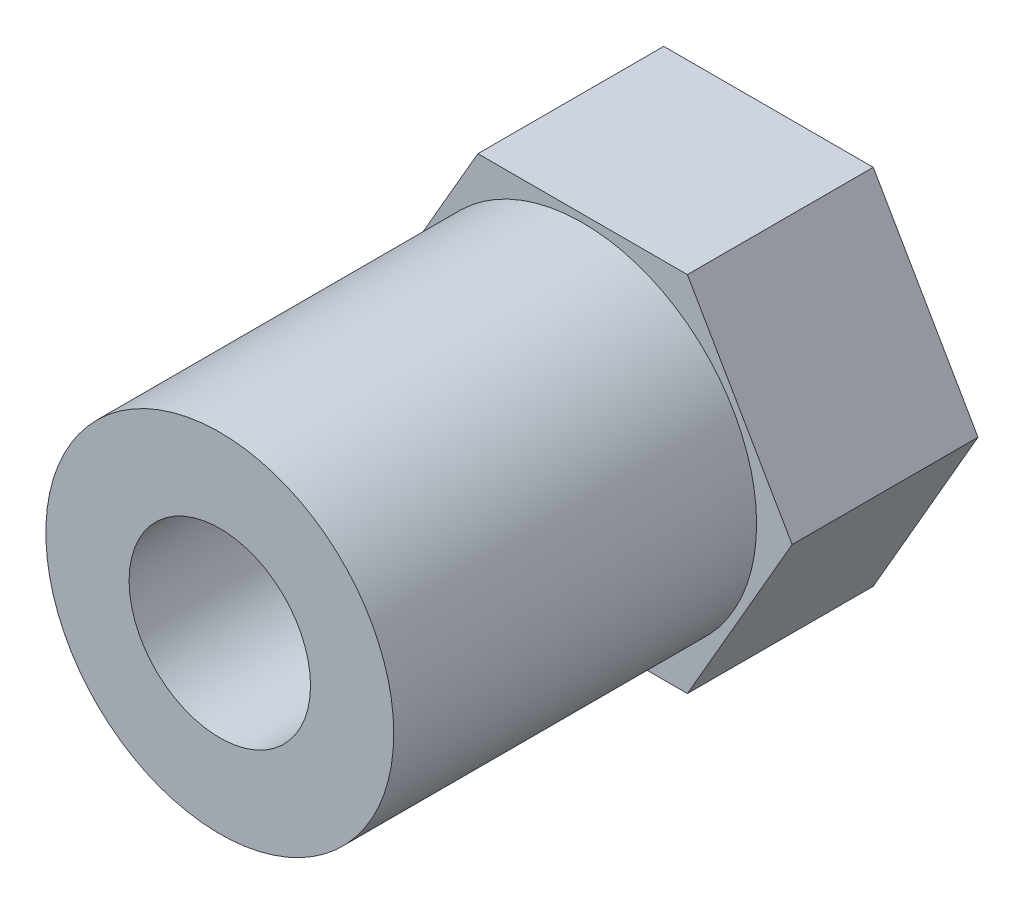
SolidWorks part; units mm, degrees
ref_plane "Front Plane" through (0, 0, 0) normal (0, 0, 1) x (1, 0, 0)
ref_plane "Top Plane" through (0, 0, 0) normal (0, 1, 0) x (1, 0, 0)
ref_plane "Right Plane" through (0, 0, 0) normal (1, 0, 0) x (0, 0, -1)
sketch "Sketch1" plane through (0, 0, 0) normal (0, 0, 1) x (1, 0, 0)
  line L1 (6.9282, 0) -> (3.4641, 6)
  line L2 (3.4641, 6) -> (-3.4641, 6)
  line L3 (-3.4641, 6) -> (-6.9282, 0)
  line L4 (-6.9282, 0) -> (-3.4641, -6)
  line L5 (-3.4641, -6) -> (3.4641, -6)
  line L6 (3.4641, -6) -> (6.9282, 0)
  circle A0 centre (0, 0) radius 6 construction
  circle A1 centre (0, 0) radius 1.6383
  dimension "D2" = 3.2766
  dimension "D1" = 12
extrude "Boss-Extrude1" add sketch "Sketch1" along normal blind 6.1468
sketch "Sketch2" plane through (0, 0, 6.1468) normal (0, 0, 1) x (1, 0, 0)
  circle A0 centre (0, 0) radius 5.7531
  circle A1 centre (0, 0) radius 3
  dimension "D1" = 11.5062
  dimension "D2" = 6
extrude "Boss-Extrude2" add sketch "Sketch2" along normal blind 12
